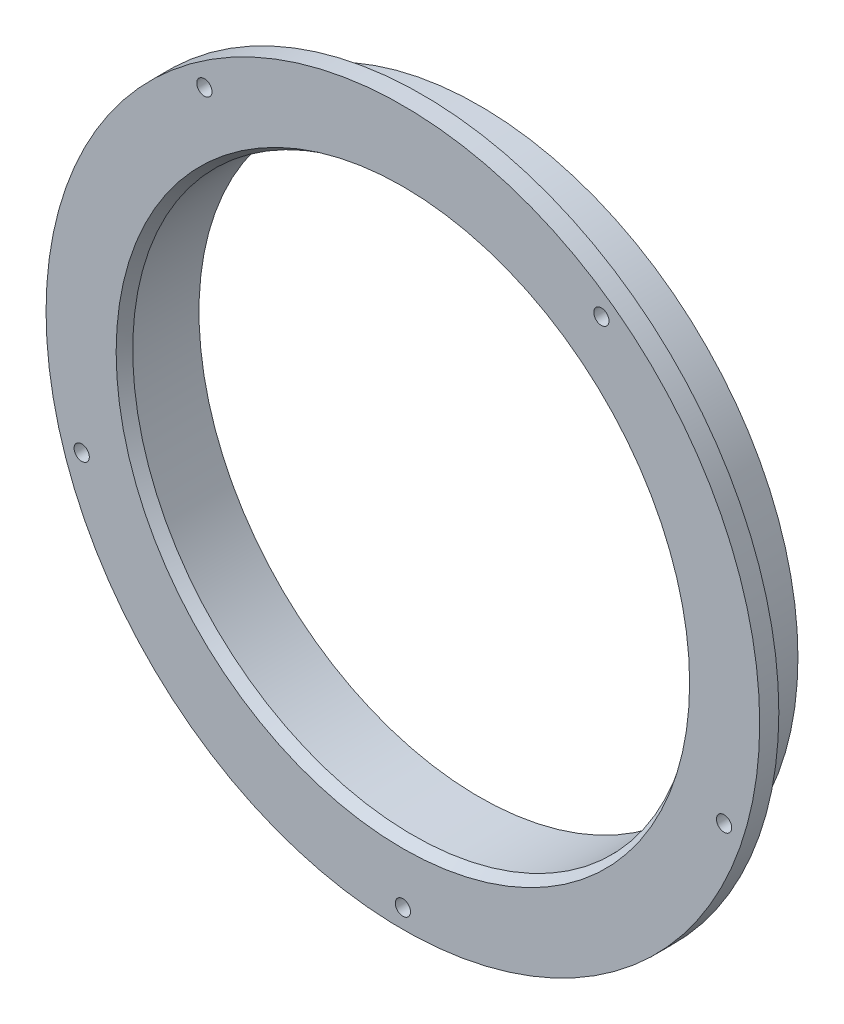
SolidWorks part; units mm, degrees
material "6061-T6 (SS)"
ref_plane "Front Plane" through (0, 0, 0) normal (0, 0, 1) x (1, 0, 0)
ref_plane "Top Plane" through (0, 0, 0) normal (0, 1, 0) x (1, 0, 0)
ref_plane "Right Plane" through (0, 0, 0) normal (1, 0, 0) x (0, 0, -1)
sketch "Sketch2" plane through (0, 0, 0) normal (1, 0, 0) x (0, 0, -1)
  line L0 (0, 0) -> (44.2866, 0) construction
  line L1 (0, 69.85) -> (19.05, 69.85)
  line L2 (0, 69.85) -> (0, 88.9)
  line L3 (0, 88.9) -> (4.7625, 88.9)
  line L4 (4.7625, 88.9) -> (4.7625, 79.375)
  line L5 (4.7625, 79.375) -> (19.05, 79.375)
  line L6 (19.05, 79.375) -> (19.05, 76.2635)
  line L7 (19.05, 76.2635) -> (6.35, 76.2635)
  line L8 (6.35, 76.2635) -> (6.35, 72.9615)
  line L9 (6.35, 72.9615) -> (19.05, 72.9615)
  line L10 (19.05, 72.9615) -> (19.05, 69.85)
  line L11 (0, 71.4375) -> (2.54, 69.85)
  line L12 (19.05, 74.6125) -> (31.6782, 74.6125) construction
  dimension "D2" = 3.302
  dimension "D3" = 139.7
  dimension "D4" = 177.8
  dimension "D5" = 12.7
  dimension "D6" = 4.7625
  dimension "D7" = 19.05
  dimension "D8" = 1.5875
  dimension "D9" = 2.54
  dimension "D10" = 149.225
revolve "Revolve1" add sketch "Sketch2" angle 360 about L0
chamfer "Chamfer1" [suppressed] distance 2.54 angle 50
hole_wizard "#6 Clearance Hole1" positions "Sketch4" profile "Sketch3" hole size "#6" standard "ANSI Inch"
sketch "Sketch4" plane through (0, 0, -4.7625) normal (0, 0, -1) x (-1, 0, 0)
  line L0 (0, 79.375) -> (0, 84.1375) construction
  line L3 (0, 84.1375) -> (0, 88.9) construction
  line L4 (0, 0) -> (0, -49.0081) construction
  line L7 (0, 0) -> (80.0195, -25.9999) construction
  line L10 (0, 0) -> (49.4548, 68.0687) construction
  circle A0 centre (0, 0) radius 84.1375
  circle A1 centre (0, 0) radius 79.375 construction
  circle A2 centre (0, 0) radius 88.9 construction
  point P0 (0, -84.1375)
  point P24 (80.0195, -25.9999)
  point P26 (49.4548, 68.0687)
  point P48 (-80.0195, -25.9999)
  point P49 (-49.4548, 68.0687)
  dimension "D1" = 72
  dimension "D2" = 72
sketch "Sketch3" plane through (0, -84.1375, -4.7625) normal (1, 0, 0) x (0, 1, 0)
  line L0 (0, 0) -> (0, 26.5408)
  line L1 (0, 26.5408) -> (1.8986, 25.4)
  line L2 (1.8986, 25.4) -> (1.8986, 0)
  line L5 (1.8986, 0) -> (0, 0)
  line L10 (0, 26.5408) -> (-1.8986, 25.4) construction
  line L11 (0, -6.35) -> (0, 107.95) construction
  dimension "Hole Dia." = 3.7973
  dimension "Hole Depth" = 25.4
  dimension "Drill Angle" = 118
